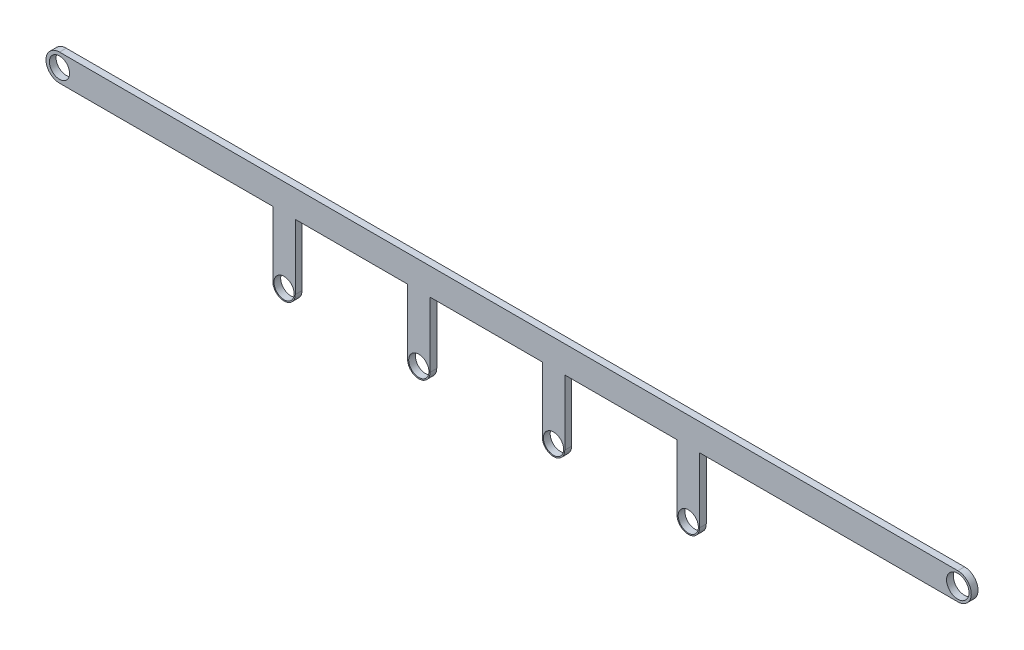
SolidWorks part; units mm, degrees
ref_plane "Front Plane" through (0, 0, 0) normal (0, 0, 1) x (1, 0, 0)
ref_plane "Top Plane" through (0, 0, 0) normal (0, 1, 0) x (1, 0, 0)
ref_plane "Right Plane" through (0, 0, 0) normal (1, 0, 0) x (0, 0, -1)
sketch "Sketch1" plane through (0, 0, 0) normal (0, 0, 1) x (1, 0, 0)
  line L0 (280, 0) -> (280, -35) construction
  line L1 (0, 6) -> (400, 6)
  line L4 (285, 0) -> (285, -35)
  line L5 (275, 0) -> (275, -35)
  line L6 (285, -6) -> (400, -6)
  line L13 (0, -6) -> (95, -6)
  line L14 (220, 0) -> (220, -35) construction
  line L15 (225, 0) -> (225, -35)
  line L16 (215, 0) -> (215, -35)
  line L17 (160, 0) -> (160, -35) construction
  line L18 (165, 0) -> (165, -35)
  line L19 (155, 0) -> (155, -35)
  line L20 (100, 0) -> (100, -35) construction
  line L21 (105, 0) -> (105, -35)
  line L22 (95, 0) -> (95, -35)
  line L23 (105, -6) -> (155, -6)
  line L24 (165, -6) -> (215, -6)
  line L25 (225, -6) -> (275, -6)
  circle A0 centre (0, 0) radius 4.5
  arc A1 (0, 6) -> (0, -6) centre (0, 0) ccw
  arc A2 (400, -6) -> (400, 6) centre (400, 0) ccw
  circle A3 centre (400, 0) radius 5
  arc A16 (285, 0) -> (275, 0) centre (280, 0) ccw
  arc A17 (275, -35) -> (285, -35) centre (280, -35) ccw
  circle A18 centre (280, -35) radius 0.375
  circle A19 centre (280, -35) radius 4.5
  circle A20 centre (220, -35) radius 4.5
  arc A21 (225, 0) -> (215, 0) centre (220, 0) ccw
  arc A22 (215, -35) -> (225, -35) centre (220, -35) ccw
  circle A23 centre (160, -35) radius 4.5
  arc A24 (165, 0) -> (155, 0) centre (160, 0) ccw
  arc A25 (155, -35) -> (165, -35) centre (160, -35) ccw
  circle A26 centre (100, -35) radius 4.5
  arc A27 (105, 0) -> (95, 0) centre (100, 0) ccw
  arc A28 (95, -35) -> (105, -35) centre (100, -35) ccw
  point P19 (280, -17.5)
  point P27 (220, -17.5)
  point P36 (160, -17.5)
  point P45 (100, -17.5)
  dimension "D1" = 9
  dimension "D2" = 9
  dimension "D7" = 0.75
  dimension "D3" = 10
  dimension "D5" = 6
  dimension "D6" = 4
  dimension "D8" = 120
  dimension "D9" = 5
  dimension "D4" = 400
  dimension "D10" = 35
extrude "Boss-Extrude2" add sketch "Sketch1" along normal blind 3
